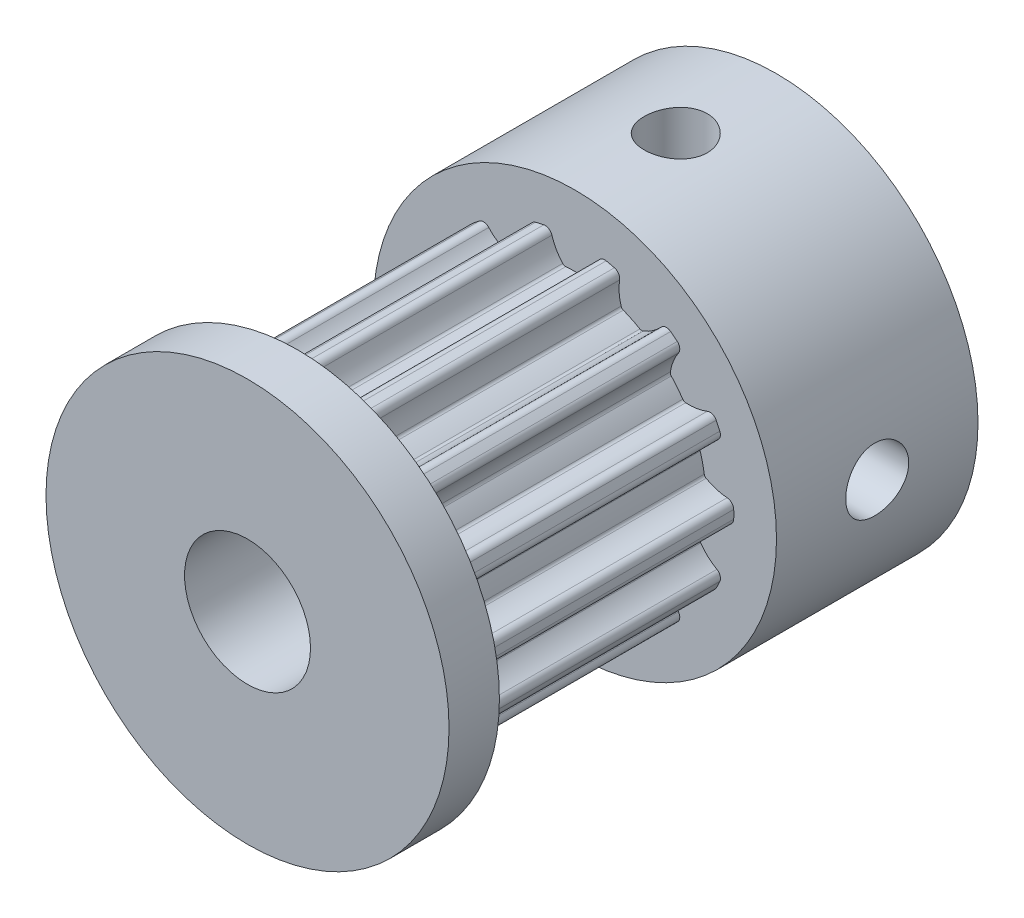
SolidWorks part; units mm, degrees
material "6061-T6 (SS)"
ref_plane "前基準面" through (0, 0, 0) normal (0, 0, 1) x (1, 0, 0)
ref_plane "上基準面" through (0, 0, 0) normal (0, 1, 0) x (1, 0, 0)
ref_plane "右基準面" through (0, 0, 0) normal (1, 0, 0) x (0, 0, -1)
sketch "草圖1" plane through (0, 0, 0) normal (0, 0, 1) x (1, 0, 0)
  circle A0 centre (0, 0) radius 6.305
  dimension "D1" = 12.61
extrude "填料-伸長1" add sketch "草圖1" along normal mid plane 11
sketch "草圖2" plane through (0, 0, 5.5) normal (0, 0, 1) x (1, 0, 0)
  line L0 (0, 0) -> (0, 6.559) construction
  line L1 (-0.975, 6.559) -> (0.975, 6.559) construction
  arc A0 (-0.3652, 5.1821) -> (0.3652, 5.1821) centre (0, 0) cw
  circle A1 centre (0, 0) radius 6.305 construction
  arc A2 (-1.2389, 6.1821) -> (-0.9158, 5.9884) centre (-1.1839, 5.9075) cw
  arc A3 (-0.9158, 5.9884) -> (-0.4868, 5.2309) centre (0.975, 6.559) ccw
  arc A4 (-0.4868, 5.2309) -> (-0.3652, 5.1821) centre (-0.3758, 5.3318) ccw
  arc A5 (0.4868, 5.2309) -> (0.3652, 5.1821) centre (0.3758, 5.3318) cw
  arc A6 (0.9158, 5.9884) -> (0.4868, 5.2309) centre (-0.975, 6.559) cw
  arc A7 (1.2389, 6.1821) -> (0.9158, 5.9884) centre (1.1839, 5.9075) ccw
  point P6 (0, 5.195)
  point P18 (0, 6.305)
  dimension "D1" = 1.11
  dimension "D2" = 0.15
  dimension "D3" = 1.975
  dimension "D4" = 0.28
  dimension "D5" = 1.95
  dimension "D6" = 0.254
extrude "除料-伸長1" cut sketch "草圖2" against normal through all and the other way through all flip side to cut
pattern_circular "環狀複製排列1" count 14 over 360 about axis through (0, 0, 5.5) along (0, 0, 1) of "除料-伸長1"
sketch "草圖3" plane through (0, 0, 5.5) normal (0, 0, 1) x (1, 0, 0)
  circle A0 centre (0, 0) radius 8
  dimension "D1" = 16
extrude "填料-伸長2" add sketch "草圖3" along normal blind 2
sketch "草圖5" plane through (0, 0, -5.5) normal (0, 0, -1) x (-1, 0, 0)
  circle A0 centre (0, 0) radius 8
  circle A1 centre (0, 0) radius 8 construction
extrude "填料-伸長3" add sketch "草圖5" along normal blind 8
sketch "草圖4" plane through (0, 0, 7.5) normal (0, 0, 1) x (1, 0, 0)
  circle A0 centre (0, 0) radius 2.5
  dimension "D1" = 5
extrude "除料-伸長2" cut sketch "草圖4" against normal through all
hole_wizard "M3x0.5 螺紋孔1" positions "草圖6" profile "草圖7" tap size "M3x0.5" standard "Ansi Metric"
sketch "草圖6" plane through (0, 0, 0) normal (0, 1, 0) x (1, 0, 0)
  line L0 (0, 13.5) -> (0, 5.5) construction
  line L1 (2.5, 13.5) -> (-2.5, 13.5) construction
  line L2 (-0.3652, 5.5) -> (0.3652, 5.5) construction
  point P0 (0, 9.5)
sketch "草圖7" plane through (0, 0, -9.5) normal (1, 0, 0) x (0, 0, -1)
  line L0 (0, 0) -> (0, 8)
  line L1 (0, 8) -> (1.25, 8)
  line L2 (1.25, 8) -> (1.25, 0)
  line L5 (1.25, 0) -> (0, 0)
  line L11 (0, -6.35) -> (0, 107.95) construction
  dimension "貫穿螺孔鑽直徑" = 2.5
  dimension "貫穿螺孔鑽深度" = 8
pattern_circular "環狀複製排列2" count 2 every 90 about axis through (0, 0, -13.5) along (0, 0, -1) of "M3x0.5 螺紋孔1"
